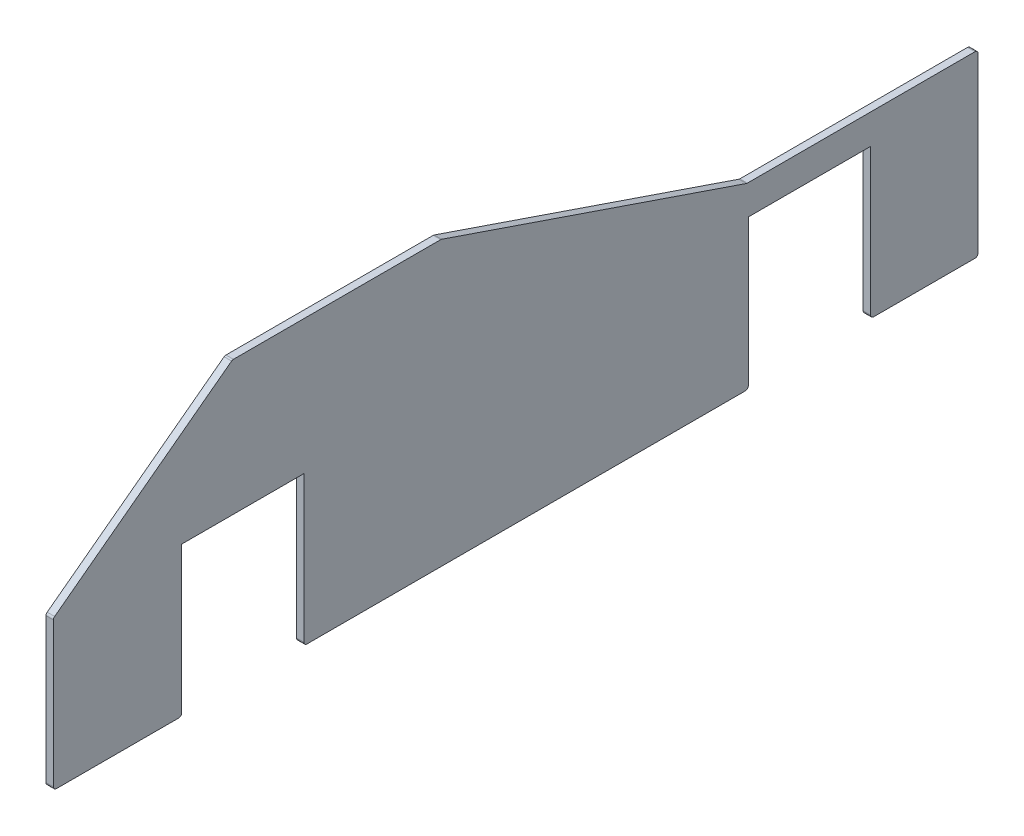
SolidWorks part; units mm, degrees
ref_plane "前视基准面" through (0, 0, 0) normal (0, 0, 1) x (1, 0, 0)
ref_plane "上视基准面" through (0, 0, 0) normal (0, 1, 0) x (1, 0, 0)
ref_plane "右视基准面" through (0, 0, 0) normal (1, 0, 0) x (0, 0, -1)
sketch "Sketch1" plane through (0, 0, 0) normal (1, 0, 0) x (0, 0, -1)
  line L1 (-310, -95) -> (310, -95)
  line L2 (-310, -95) -> (-310, 95)
  line L3 (-310, 95) -> (310, 95)
  line L4 (310, -95) -> (310, 95)
  line L5 (-310, -95) -> (310, 95) construction
  line L6 (-310, 95) -> (310, -95) construction
  point P0 (0, 0)
  dimension "D1" = 620
  dimension "D2" = 190
extrude "Boss-Extrude1" add sketch "Sketch1" along normal blind 5
sketch "Sketch2" plane through (5, 0, 0) normal (1, 0, 0) x (0, 0, -1)
  line L0 (-310, -95) -> (310, -95) construction
  line L1 (-224, -95) -> (-142, -95)
  line L2 (-224, -95) -> (-224, 5)
  line L3 (-224, 5) -> (-142, 5)
  line L4 (-142, -95) -> (-142, 5)
  line L5 (-310, 95) -> (-310, -95) construction
  line L6 (156, -95) -> (238, -95)
  line L7 (156, -95) -> (156, 5)
  line L8 (156, 5) -> (238, 5)
  line L9 (238, -95) -> (238, 5)
  line L10 (310, -95) -> (310, 95) construction
  line L11 (-310, 5) -> (-190, 95)
  line L12 (310, 95) -> (-310, 95) construction
  line L13 (-50, 95) -> (155, 25)
  line L14 (155, 25) -> (310, 25)
  line M9 (310, -95) -> (310, 95)
  line M10 (310, 95) -> (-310, 95)
  line M11 (-310, 95) -> (-310, -95)
  line M12 (-310, -95) -> (310, -95)
  dimension "D1" = 100
  dimension "D2" = 100
  dimension "D3" = 82
  dimension "D4" = 82
  dimension "D5" = 86
  dimension "D6" = 72
  dimension "D7" = 360
  dimension "D8" = 20
  dimension "D9" = 155
  dimension "D10" = 100
  dimension "D11" = 120
extrude "Cut-Extrude1" cut sketch "Sketch2" against normal blind 5 contours L11 M11 M10 | L13 L14 M9 M10 | L4 L3 L2 M12 | L9 L8 L7 M12
fillet "Fillet1" radius 2 11 edges at (2.5, 95, 50) (2.5, 5, 310) (2.5, -95, 310) (2.5, -95, 224) (2.5, -95, 142) (2.5, -95, -156) (2.5, -95, -238) (2.5, -95, -310) (2.5, 25, -310) (2.5, 25, -155) (2.5, 95, 190)
